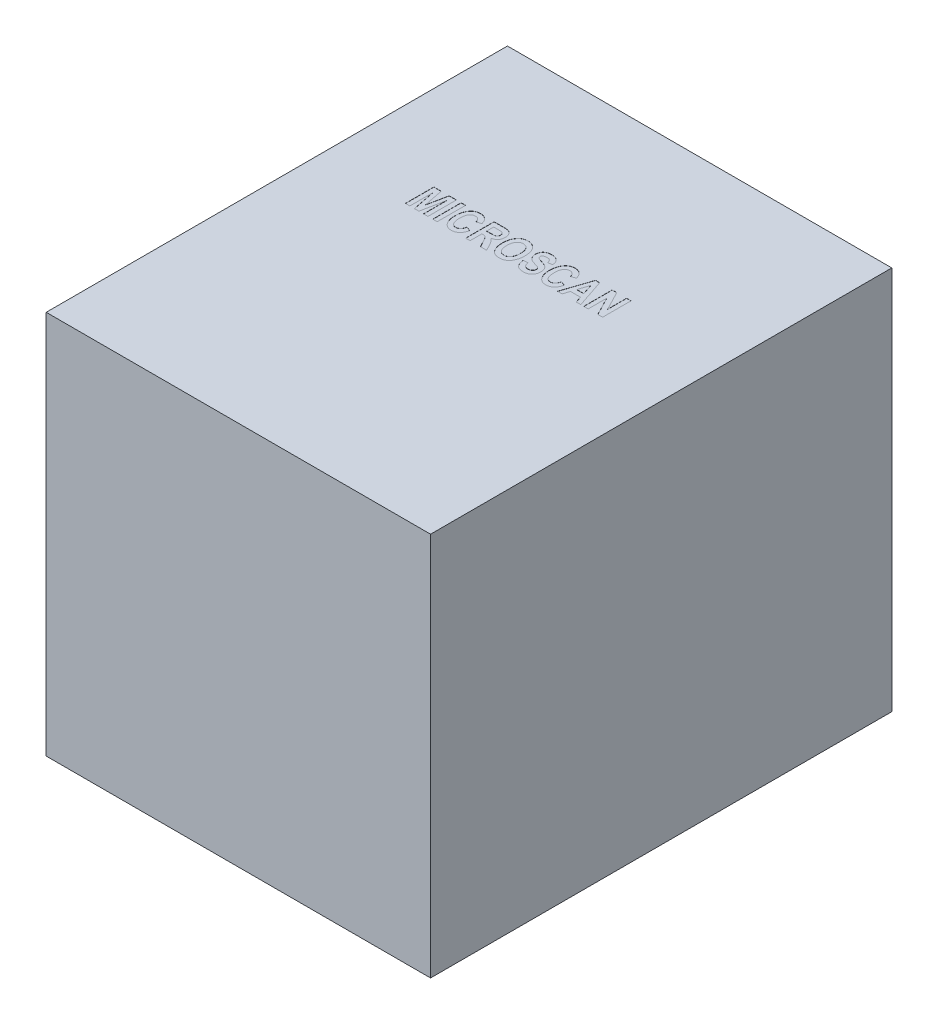
SolidWorks part; units mm, degrees
ref_plane "Front Plane" through (0, 0, 0) normal (0, 0, 1) x (1, 0, 0)
ref_plane "Top Plane" through (0, 0, 0) normal (0, 1, 0) x (1, 0, 0)
ref_plane "Right Plane" through (0, 0, 0) normal (1, 0, 0) x (0, 0, -1)
sketch "Sketch1" plane through (0, 0, 0) normal (0, 0, 1) x (1, 0, 0)
  line L1 (125, -125) -> (-125, -125)
  line L2 (125, -125) -> (125, 125)
  line L3 (125, 125) -> (-125, 125)
  line L4 (-125, -125) -> (-125, 125)
  line L5 (125, -125) -> (-125, 125) construction
  line L6 (125, 125) -> (-125, -125) construction
  point P0 (0, 0)
  dimension "D1" = 250
  dimension "D2" = 250
extrude "Boss-Extrude1" add sketch "Sketch1" along normal blind 300
sketch "Sketch2" plane through (0, 125, 0) normal (0, 1, 0) x (1, 0, 0)
  text T0 "MICROSCAN" font "Arial Narrow" height in points 72
extrude "Cut-Extrude1" cut sketch "Sketch2" against normal blind 0.1
